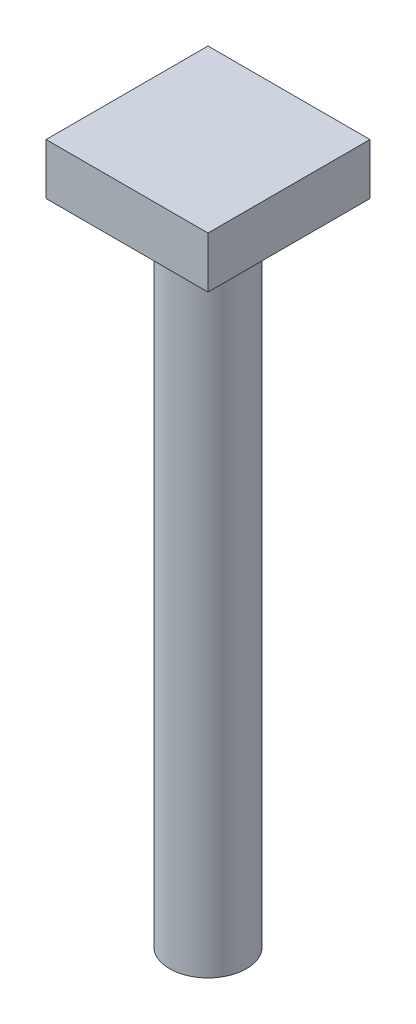
SolidWorks part; units mm, degrees
ref_plane "Front Plane" through (0, 0, 0) normal (0, 0, 1) x (1, 0, 0)
ref_plane "Top Plane" through (0, 0, 0) normal (0, 1, 0) x (1, 0, 0)
ref_plane "Right Plane" through (0, 0, 0) normal (1, 0, 0) x (0, 0, -1)
sketch "Sketch2" plane through (0, 0, 0) normal (0, 1, 0) x (1, 0, 0)
  line L1 (9.5, 9.5) -> (-9.5, 9.5)
  line L2 (9.5, 9.5) -> (9.5, -9.5)
  line L3 (9.5, -9.5) -> (-9.5, -9.5)
  line L4 (-9.5, 9.5) -> (-9.5, -9.5)
  line L5 (9.5, 9.5) -> (-9.5, -9.5) construction
  line L6 (9.5, -9.5) -> (-9.5, 9.5) construction
  point P0 (0, 0)
  dimension "D1" = 19
extrude "Boss-Extrude1" add sketch "Sketch2" along normal blind 6
sketch "Sketch3" plane through (0, 0, 0) normal (0, -1, 0) x (-1, 0, 0)
  circle A0 centre (0, 0) radius 4.5
  dimension "D1" = 9
extrude "Boss-Extrude2" add sketch "Sketch3" along normal blind 76
